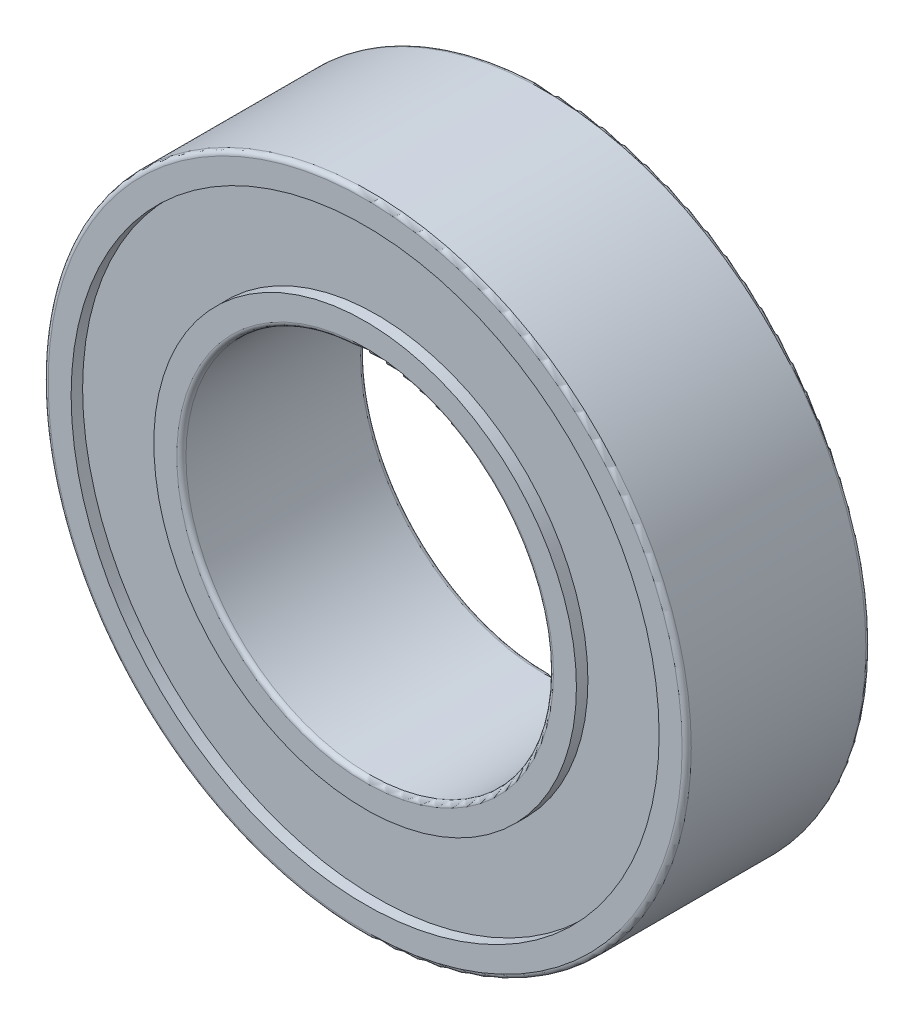
SolidWorks part; units mm, degrees
ref_plane "Front Plane" through (0, 0, 0) normal (0, 0, 1) x (1, 0, 0)
ref_plane "Top Plane" through (0, 0, 0) normal (0, 1, 0) x (1, 0, 0)
ref_plane "Right Plane" through (0, 0, 0) normal (1, 0, 0) x (0, 0, -1)
sketch "Sketch1" plane through (0, 0, 0) normal (0, 0, 1) x (1, 0, 0)
  circle A0 centre (0, 0) radius 4
  circle A1 centre (0, 0) radius 7
  dimension "D1" = 8
  dimension "D2" = 14
extrude "Boss-Extrude1" add sketch "Sketch1" along normal blind 4
sketch "Sketch2" plane through (0, 0, 4) normal (0, 0, 1) x (1, 0, 0)
  circle A0 centre (0, 0) radius 4.6
  circle A1 centre (0, 0) radius 6.4
  circle A2 centre (0, 0) radius 4 construction
  circle A3 centre (0, 0) radius 7 construction
  dimension "D1" = 0.6
  dimension "D2" = 0.6
extrude "Cut-Extrude1" cut sketch "Sketch2" against normal blind 0.25
sketch "Sketch3" plane through (0, 0, 0) normal (0, 0, -1) x (-1, 0, 0)
  circle A0 centre (0, 0) radius 4.6
  circle A1 centre (0, 0) radius 6.4
  circle A2 centre (0, 0) radius 7 construction
  circle A3 centre (0, 0) radius 4 construction
  dimension "D1" = 0.6
  dimension "D2" = 0.6
extrude "Cut-Extrude2" cut sketch "Sketch3" against normal blind 0.25
fillet "Fillet1" radius 0.1 2 edges at (7, 0, 0) (7, 0, 4)
fillet "Fillet2" radius 0.1 2 edges at (4, 0, 4) (4, 0, 0)
